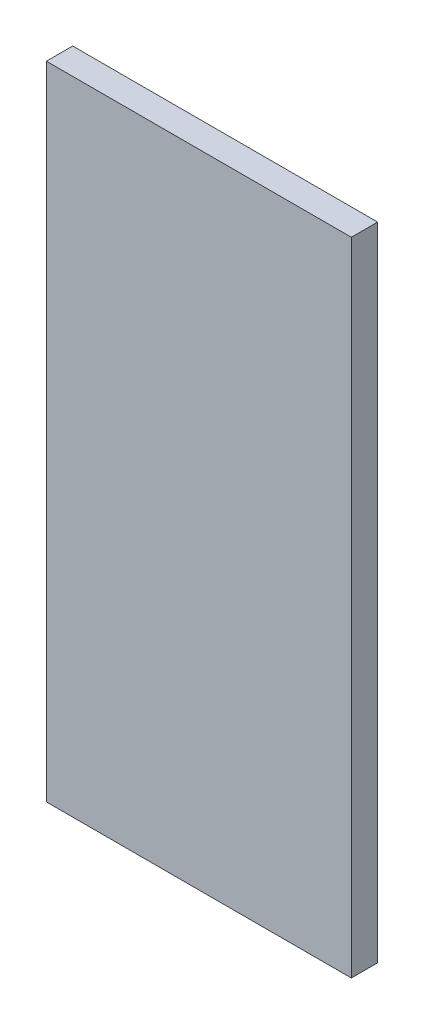
SolidWorks part; units mm, degrees
material "1060 Alloy"
ref_plane "Front Plane" through (0, 0, 0) normal (0, 0, 1) x (1, 0, 0)
ref_plane "Top Plane" through (0, 0, 0) normal (0, 1, 0) x (1, 0, 0)
ref_plane "Right Plane" through (0, 0, 0) normal (1, 0, 0) x (0, 0, -1)
sketch "Sketch2" plane through (0, 0, 0) normal (0, 0, 1) x (1, 0, 0)
  line L1 (-145, -305) -> (145, -305)
  line L2 (-145, -305) -> (-145, 305)
  line L3 (-145, 305) -> (145, 305)
  line L4 (145, -305) -> (145, 305)
  line L5 (-145, -305) -> (145, 305) construction
  line L6 (-145, 305) -> (145, -305) construction
  point P0 (0, 0)
  dimension "D1" = 290
  dimension "D2" = 610
extrude "Boss-Extrude1" add sketch "Sketch2" along normal blind 25
